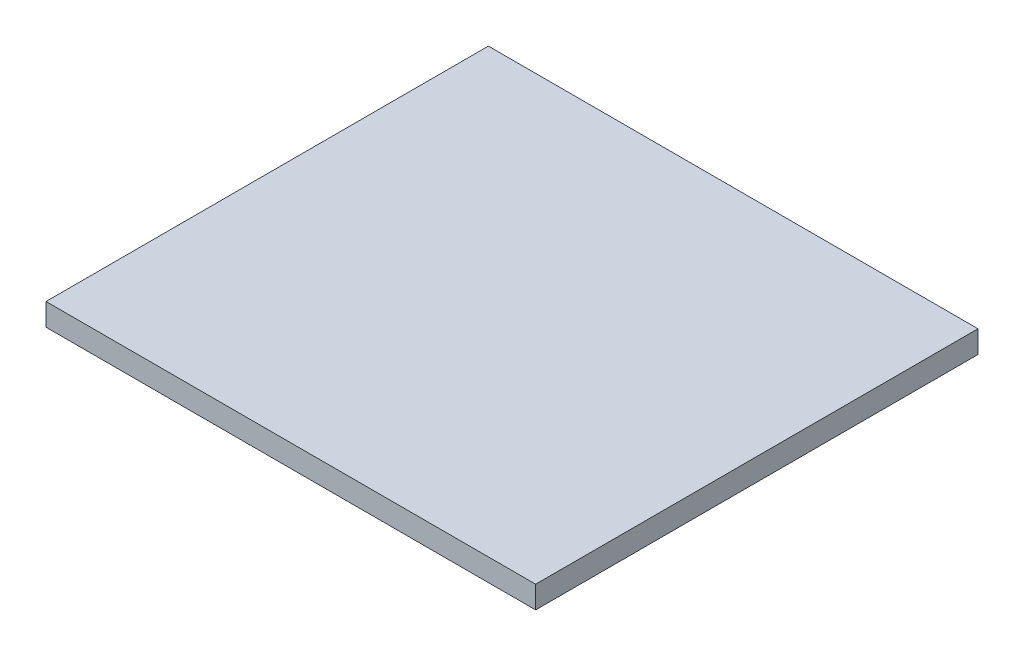
SolidWorks part; units mm, degrees
material "6061 Alloy"
ref_plane "Front Plane" through (0, 0, 0) normal (0, 0, 1) x (1, 0, 0)
ref_plane "Top Plane" through (0, 0, 0) normal (0, 1, 0) x (1, 0, 0)
ref_plane "Right Plane" through (0, 0, 0) normal (1, 0, 0) x (0, 0, -1)
sketch "Sketch1" plane through (0, 0, 0) normal (0, 1, 0) x (1, 0, 0)
  line L1 (-62.4198, -54.6642) -> (77.0262, -54.6642)
  line L2 (-62.4198, -54.6642) -> (-62.4198, 71.3198)
  line L3 (-62.4198, 71.3198) -> (77.0262, 71.3198)
  line L4 (77.0262, -54.6642) -> (77.0262, 71.3198)
  dimension "D1" = 139.446
  dimension "D2" = 125.984
extrude "Boss-Extrude1" add sketch "Sketch1" along normal blind 6.35
